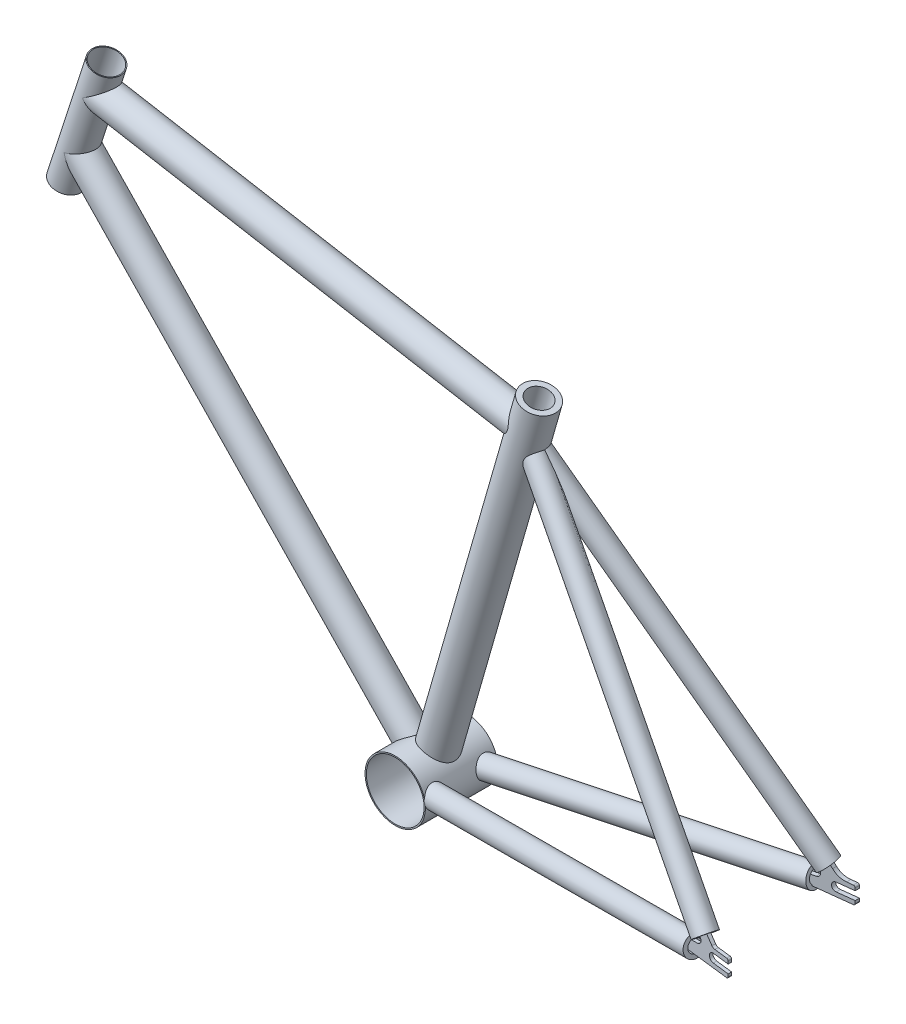
SolidWorks part; units mm, degrees
ref_plane "Front Plane" through (0, 0, 0) normal (0, 0, 1) x (1, 0, 0)
ref_plane "Top Plane" through (0, 0, 0) normal (0, 1, 0) x (1, 0, 0)
ref_plane "Right Plane" through (0, 0, 0) normal (1, 0, 0) x (0, 0, -1)
sketch "Sketch2" plane through (0, 0, 0) normal (0, 0, 1) x (1, 0, 0)
  line L0 (-416.6903, 0) -> (1544.5173, 0) construction
  line L1 (-416.6903, -50) -> (1544.5173, -50) construction
  line L2 (568.5168, -50) -> (985.53, 0)
  line L3 (985.53, 0) -> (682.4065, 347.1804)
  line L4 (568.5168, -50) -> (695.31, 392.1804)
  line L5 (175.2739, 447.1071) -> (685.2739, 357.1804)
  line L6 (568.5168, -50) -> (153.6427, 380.5332)
  line L7 (139.737, 337.7356) -> (186.0895, 480.3941)
  line L8 (-40.5504, -217.1318) -> (262.2413, 714.7653) construction
  line L9 (-416.6903, -331) -> (1545.0178, -331) construction
  circle A0 centre (30, 0) radius 331 construction
  circle A1 centre (985.53, 0) radius 331 construction
  point P19 (30, 0)
  dimension "D1" = 50
  dimension "D2" = 420
  dimension "D3" = 460
  dimension "D4" = 74
  dimension "D5" = 10
  dimension "D6" = 35
  dimension "D7" = 510
  dimension "D8" = 35
  dimension "D9" = 45
  dimension "D10" = 150
  dimension "D11" = 72
  dimension "D12" = 82
  dimension "D13" = 30
  dimension "D14" = 331
ref_plane "Plane1" through (186.0895, 480.3941, 0) normal (0.309, 0.9511, 0) x (0.9511, -0.309, 0)
sketch "Sketch3" plane through (186.0895, 480.3941, 0) normal (0.309, 0.9511, 0) x (0.9511, -0.309, 0)
  circle A0 centre (0, 0) radius 17.5
  circle A1 centre (0, 0) radius 16.5
  dimension "D1" = 35
  dimension "D2" = 33
extrude "Boss-Extrude1" add sketch "Sketch3" against normal up to vertex (150 mm away) up to point (139.737, 337.7356, 0)
ref_plane "Plane2" through (695.31, 392.1804, 0) normal (0.2756, 0.9613, 0) x (0.9613, -0.2756, 0)
sketch "Sketch4" plane through (695.31, 392.1804, 0) normal (0.2756, 0.9613, 0) x (0.9613, -0.2756, 0)
  circle A0 centre (0, 0) radius 20
  circle A1 centre (0, 0) radius 13.6
  dimension "D1" = 40
  dimension "D2" = 27.2
sketch "Sketch5" plane through (0, 0, 0) normal (0, 0, 1) x (1, 0, 0)
  line L0 (175.2739, 447.1071) -> (685.2739, 357.1804) construction
  line L1 (568.5168, -50) -> (153.6427, 380.5332) construction
  circle A0 centre (568.5168, -50) radius 35.5
  circle A1 centre (568.5168, -50) radius 34
  point P4 (430.2739, 402.1438)
  point P5 (361.0798, 165.2666)
  dimension "D1" = 71
  dimension "D2" = 68
extrude "Boss-Extrude2" add sketch "Sketch5" along normal mid plane 85 separate body
extrude "Boss-Extrude3" add sketch "Sketch4" against normal up to surface (430.67 mm away) separate body
ref_plane "Plane3" through (430.2739, 402.1438, 0) normal (0.9848, -0.1736, 0) x (0, 0, -1)
sketch "Sketch6" plane through (430.2739, 402.1438, 0) normal (0.9848, -0.1736, 0) x (0, 0, -1)
  circle A0 centre (0, 0) radius 17.5
  circle A1 centre (0, 0) radius 10
  dimension "D1" = 20
  dimension "D2" = 35
extrude "Boss-Extrude5" add sketch "Sketch6" along normal up to surface (240.663 mm away)
sketch "Sketch7" plane through (430.2739, 402.1438, 0) normal (0.9848, -0.1736, 0) x (0, 0, -1)
  circle A1 centre (0, 0) radius 10
  circle A2 centre (0, 0) radius 10
  circle A3 centre (0, 0) radius 17.5
  circle A4 centre (0, 0) radius 17.5
  dimension "D1" = 0
  dimension "D2" = 0
extrude "Boss-Extrude6" add sketch "Sketch7" against normal up to surface (239.8564 mm away)
ref_plane "Plane4" through (361.0798, 165.2666, 0) normal (-0.6939, 0.7201, 0) x (0.7201, 0.6939, 0)
sketch "Sketch8" plane through (361.0798, 165.2666, 0) normal (-0.6939, 0.7201, 0) x (0.7201, 0.6939, 0)
  circle A0 centre (0, 0) radius 10
  circle A1 centre (0, 0) radius 17.5
  dimension "D1" = 35
  dimension "D2" = 20
extrude "Boss-Extrude7" add sketch "Sketch8" along normal up to surface (273.7859 mm away)
sketch "Sketch9" plane through (361.0798, 165.2666, 0) normal (-0.6939, 0.7201, 0) x (0.7201, 0.6939, 0)
  circle A1 centre (0, 0) radius 17.5
  circle A2 centre (0, 0) radius 17.5
  circle A3 centre (0, 0) radius 10
  circle A4 centre (0, 0) radius 10
  dimension "D1" = 0
  dimension "D2" = 0
extrude "Boss-Extrude8" add sketch "Sketch9" against normal up to surface (268.061 mm away)
sketch "Sketch10" plane through (0, 0, 0) normal (0, 1, 0) x (1, 0, 0)
  line L0 (558.0168, 65.7995) -> (558.0168, -64.743) construction
  line L1 (602.5168, 42.5) -> (534.5168, 42.5) construction
  line L2 (-416.6903, 0) -> (1545.0178, 0) construction
  line L3 (533.0168, 42.5) -> (533.0168, -42.5) construction
  line L5 (558.0168, 25) -> (985.53, 75)
  line L6 (985.53, 75) -> (985.53, -75)
  line L7 (985.53, -75) -> (558.0168, -25)
  dimension "D1" = 25
  dimension "D2" = 25
  dimension "D3" = 50
  dimension "D4" = 150
ref_plane "Plane5" through (4.6454, 0, -39.7198) normal (0.1162, 0, -0.9932) x (-0.9932, 0, -0.1162)
sketch "Sketch11" plane through (4.6454, 0, -39.7198) normal (0.1162, 0, -0.9932) x (-0.9932, 0, -0.1162)
  line L0 (-1113.4179, -22.2286) -> (-903.6196, -22.2286) construction
  line L1 (413.8694, 0) -> (-1534.0611, 0) construction
  line L5 (-996.5215, -10) -> (-952.0977, -10)
  line L6 (-940.113, -10.7208) -> (-892.4438, -16.4753)
  line L7 (-998.5215, -8) -> (-998.5215, 8)
  line L8 (-891.0056, -4.5618) -> (-957.5792, 3.4748)
  line L9 (-960.7575, 11.7146) -> (-921.4481, 57.0442)
  line L11 (-930.514, 64.9061) -> (-976.6328, 11.7242)
  line L12 (-980.4102, 10) -> (-996.5215, 10)
  line L14 (-930.514, 64.9061) -> (-921.4481, 57.0442)
  line L15 (-978.8581, 0) -> (-677.7866, 347.1804) construction
  line L16 (-564.668, -50) -> (-978.8581, 0) construction
  line L17 (-891.0056, -4.5618) -> (-892.4438, -16.4753)
  arc A1 (-998.5215, -8) -> (-996.5215, -10) centre (-996.5215, -8) ccw
  arc A4 (-996.5215, 10) -> (-998.5215, 8) centre (-996.5215, 8) ccw
  arc A5 (-957.5792, 3.4748) -> (-960.7575, 11.7146) centre (-956.98, 8.4388) cw
  arc A6 (-976.6328, 11.7242) -> (-980.4102, 10) centre (-980.4102, 15) cw
  arc A7 (-952.0977, -10) -> (-940.113, -10.7208) centre (-952.0977, -110) cw
  point P11 (-965.2904, 15.6455)
  point P14 (-951.2923, -3.3277)
  point P31 (-998.5215, -10)
  point P34 (-998.5215, -5)
  point P37 (-998.5215, 5)
  point P40 (-998.5215, 10)
  dimension "D8" = 2
  dimension "D9" = 5
  dimension "D10" = 100
  dimension "D2" = 5
  dimension "D3" = 5
  dimension "D4" = 10
  dimension "D6" = 12
  dimension "D7" = 12
  dimension "D11" = 60
  dimension "D12" = 60
  dimension "D13" = 12
  dimension "D14" = 6
  dimension "D15" = 6
  dimension "D16" = 60
  dimension "D17" = 60
extrude "Boss-Extrude9" add sketch "Sketch11" along normal mid plane 4 separate body
ref_plane "Plane6" through (0, -50, 0) normal (0, 1, 0) x (1, 0, 0)
sketch "Sketch12" plane through (0, -50, 0) normal (0, 1, 0) x (1, 0, 0)
  line L0 (558.0168, 65.7995) -> (558.0168, -64.743) construction
  line L1 (558.0168, 65.7995) -> (558.0168, -64.743) construction
sketch3d "3DSketch1"
  line L0 (682.4065, 347.1804, 0) -> (963.4009, 15.6455, 72.4119)
  line L1 (558.0168, -50, 25) -> (949.4976, -3.3277, 70.7858) construction
  line L2 (558.0168, -50, -65.7995) -> (558.0168, -50, 64.743) construction
  dimension "D1" = 39.743
ref_plane "Plane7" through (949.4976, -3.3277, 70.7858) normal (0.9863, 0.1176, 0.1154) x (0.1145, 0.014, -0.9933)
sketch "Sketch13" plane through (949.4976, -3.3277, 70.7858) normal (0.9863, 0.1176, 0.1154) x (0.1145, 0.014, -0.9933)
  circle A0 centre (0, 0) radius 12.5
  circle A1 centre (0, 0) radius 7.5
  dimension "D1" = 15
  dimension "D2" = 25
extrude "Boss-Extrude10" add sketch "Sketch13" against normal up to surface (353.4546 mm away)
ref_plane "Plane8" through (963.4009, 15.6455, 72.4119) normal (0.6378, -0.7525, 0.1644) x (-0.7702, -0.6231, 0.1359)
sketch "Sketch14" plane through (963.4009, 15.6455, 72.4119) normal (0.6378, -0.7525, 0.1644) x (-0.7702, -0.6231, 0.1359)
  circle A0 centre (0, 0) radius 12.5
  circle A1 centre (0, 0) radius 7.5
  dimension "D1" = 15
  dimension "D2" = 25
extrude "Boss-Extrude11" add sketch "Sketch14" against normal up to surface (424.8717 mm away)
mirror "Mirror5" about plane through (0, 0, 0) normal (0, 0, 1) of "Boss-Extrude10"
mirror "Mirror7" about plane through (0, 0, 0) normal (0, 0, 1) of "Boss-Extrude11"
ref_plane "Plane10" through (4.6454, 0, 39.7198) normal (0.1162, 0, 0.9932) x (0.9932, 0, -0.1162)
sketch "Sketch17" plane through (4.6454, 0, 39.7198) normal (0.1162, 0, 0.9932) x (0.9932, 0, -0.1162)
  line L0 (1007.4077, 8.0055) -> (1007.4077, -8.0012)
  line L2 (950.3218, -10.0012) -> (1005.4077, -10.0012)
  line L7 (1005.4077, 10.0055) -> (988.9055, 10.0055)
  line L8 (1008.2019, 0) -> (993.0931, 0) construction
  line L9 (937.3381, -10.8477) -> (890.7212, -16.9519)
  line L10 (772.7368, -32.4365) -> (770.7893, -17.5635)
  line L11 (889.4943, -5.1722) -> (956.6092, 1.8181)
  line L12 (959.8687, 10.0669) -> (923.1539, 52.4046)
  line L13 (822.6561, 168.6765) -> (833.9885, 178.5039)
  line L14 (934.4863, 62.232) -> (973.7957, 16.9024)
  line L15 (978.8581, 0) -> (677.7866, 347.1804) construction
  line L16 (564.668, -50) -> (978.8581, 0) construction
  line L17 (934.4863, 62.232) -> (923.1539, 52.4046)
  line L18 (889.4943, -5.1722) -> (890.7212, -16.9519)
  arc A1 (1005.4077, -10.0012) -> (1007.4077, -8.0012) centre (1005.4077, -8.0012) ccw
  arc A4 (1007.4077, 8.0055) -> (1005.4077, 10.0055) centre (1005.4077, 8.0055) ccw
  arc A5 (988.9055, 10.0055) -> (973.7957, 16.9024) centre (988.9055, 30.0055) cw
  arc A6 (956.6092, 1.8181) -> (959.8687, 10.0669) centre (956.0912, 6.7912) ccw
  arc A7 (950.3218, -10.0012) -> (937.3381, -10.8477) centre (950.3218, -110.0012) ccw
  point P18 (1007.4193, -10)
  point P21 (1007.4193, -5)
  point P24 (1007.4193, 5)
  point P27 (1007.4193, 10)
  point P33 (828.3223, 173.5902)
  point P34 (771.763, -25)
  dimension "D6" = 2
  dimension "D7" = 2
  dimension "D10" = 20
  dimension "D11" = 5
  dimension "D12" = 100
  dimension "D2" = 5
  dimension "D3" = 5
  dimension "D8" = 15
  dimension "D9" = 15
  dimension "D13" = 60
  dimension "D14" = 60
  dimension "D15" = 15
  dimension "D16" = 11.8434
extrude "Boss-Extrude12" add sketch "Sketch17" along normal blind 5
sketch "Sketch19" plane through (0, 0, 0) normal (0, 0, 1) x (1, 0, 0)
  line L0 (994.1882, -10) -> (950.0652, -10) construction
  line L1 (996.1747, -8) -> (996.1747, 8) construction
  line L2 (976.1747, 5) -> (996.1747, 5)
  line L3 (1011.9898, 5) -> (1011.9898, -5)
  line L4 (996.1747, -5) -> (976.1747, -5)
  line L5 (996.1747, -8) -> (996.1747, -5)
  line L7 (1011.9898, -10) -> (1011.9898, -5)
  line L8 (1011.9898, 5) -> (1011.9898, 10)
  line L10 (996.1747, 5) -> (996.1747, 8)
  line L11 (994.1882, 10) -> (994.1882, 11.3302)
  line L12 (994.1882, 11.3302) -> (1011.9898, 11.3302)
  line L13 (1011.9898, 11.3302) -> (1011.9898, 10)
  line L14 (1011.9898, -10) -> (1011.9898, -11.1818)
  line L15 (1011.9898, -11.1818) -> (994.1882, -11.1818)
  line L16 (994.1882, -11.1818) -> (994.1882, -10)
  arc A0 (976.1747, 5) -> (976.1747, -5) centre (976.1747, 0) ccw
  ellipse E2 centre (994.1882, -8) end of major axis (994.1882, -10) minor radius 1.9865 (994.1882, -10) -> (996.1747, -8) ccw
  ellipse E3 centre (994.1882, 8) end of major axis (994.1882, 6) minor radius 1.9865 (996.1747, 8) -> (994.1882, 10) ccw
  dimension "D1" = 10
  dimension "D2" = 10
  dimension "D3" = 20
extrude "Cut-Extrude2" cut sketch "Sketch19" against normal mid plane 200
